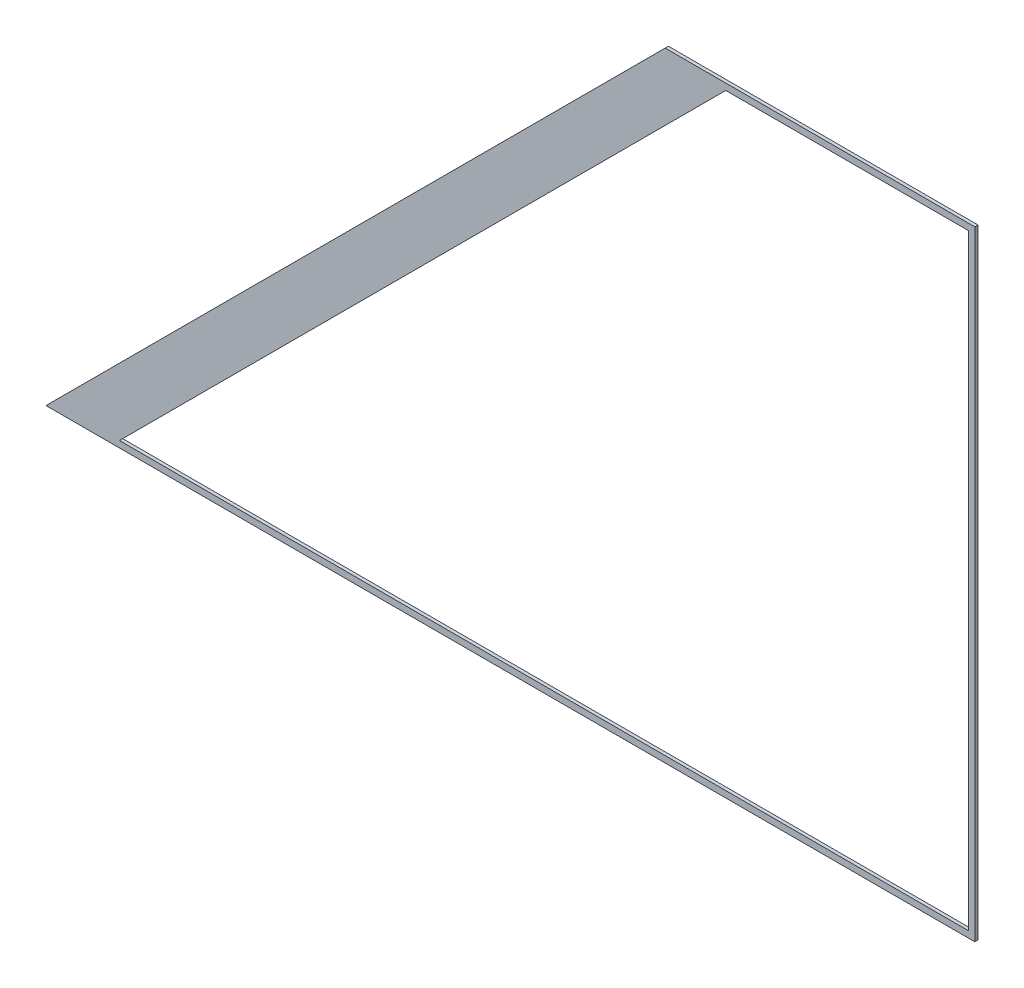
SolidWorks part; units mm, degrees
ref_plane "Front Plane" through (0, 0, 0) normal (0, 0, 1) x (1, 0, 0)
ref_plane "Top Plane" through (0, 0, 0) normal (0, 1, 0) x (1, 0, 0)
ref_plane "Right Plane" through (0, 0, 0) normal (1, 0, 0) x (0, 0, -1)
sketch "Sketch1" plane through (0, 0, 0) normal (0, 0, 1) x (1, 0, 0)
  line L0 (0, 0) -> (914.4, 0)
  line L1 (914.4, 0) -> (914.4, 609.6)
  line L2 (914.4, 609.6) -> (609.6, 609.6)
  line L3 (609.6, 609.6) -> (0, 0)
  dimension "D1" = 914.4
  dimension "D2" = 609.6
  dimension "D3" = 45
extrude "Boss-Extrude1" add sketch "Sketch1" along normal blind 3.175
sketch "Sketch2" plane through (0, 0, 3.175) normal (0, 0, 1) x (1, 0, 0)
  line L0 (72.3092, 6.35) -> (908.05, 6.35)
  line L1 (908.05, 6.35) -> (908.05, 603.25)
  line L2 (908.05, 603.25) -> (669.2092, 603.25)
  line L3 (669.2092, 603.25) -> (72.3092, 6.35)
  line L4 (0, 0) -> (914.4, 0) construction
  line L5 (914.4, 0) -> (914.4, 609.6) construction
  line L6 (914.4, 609.6) -> (609.6, 609.6) construction
  dimension "D1" = 6.35
  dimension "D2" = 6.35
  dimension "D3" = 6.35
  dimension "D4" = 45
extrude "Cut-Extrude1" cut sketch "Sketch2" against normal through all
